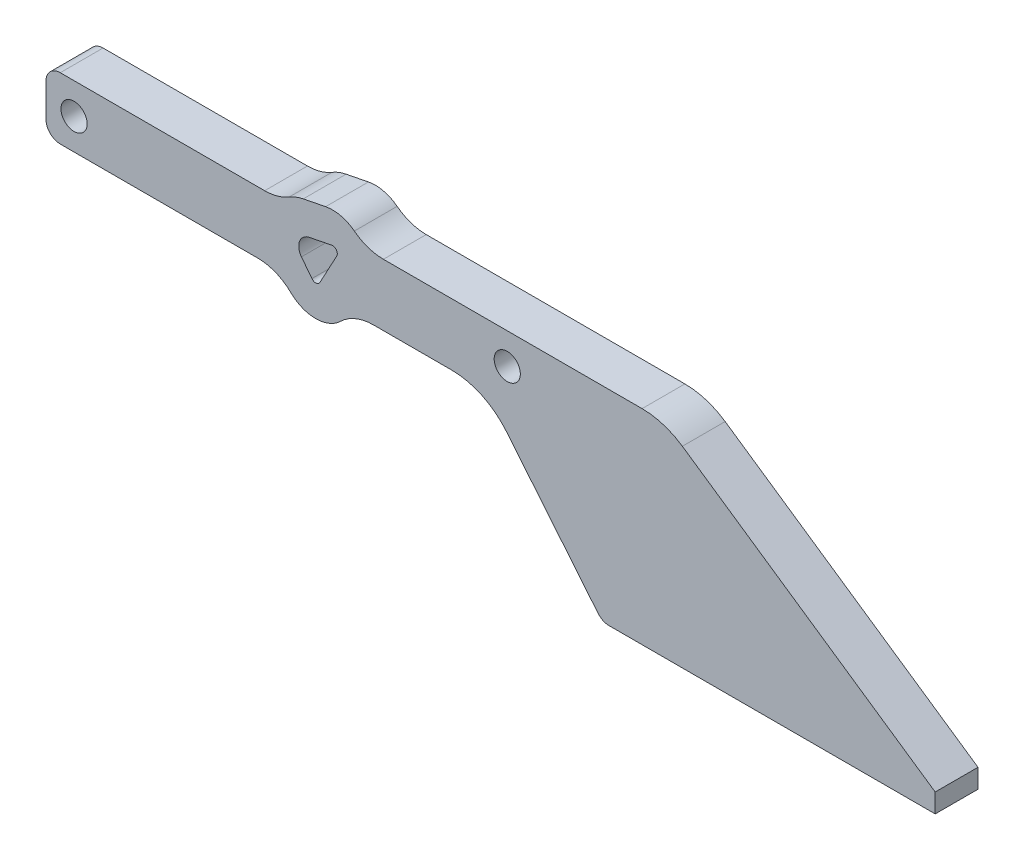
SolidWorks part; units mm, degrees
ref_plane "Front Plane" through (0, 0, 0) normal (0, 0, 1) x (1, 0, 0)
ref_plane "Top Plane" through (0, 0, 0) normal (0, 1, 0) x (1, 0, 0)
ref_plane "Right Plane" through (0, 0, 0) normal (1, 0, 0) x (0, 0, -1)
sketch "Sketch3" plane through (0, 0, 0) normal (0, 0, 1) x (1, 0, 0)
  line L6 (0, 0) -> (-70, 0)
  line L7 (-70, 0) -> (-70, 30) construction
  line L9 (-15.5885, 13) -> (-57, 13) construction
  line L15 (-57, 42.3999) -> (-57, 43) construction
  line L16 (-57, 43) -> (-187, 43)
  line L18 (-90, 30) -> (-90, 43) construction
  line L19 (-90, 36.5) -> (-90, -3.5) construction
  line L20 (-90, -3.5) -> (-131.1, -3.5) construction
  line L21 (-131.1, -3.5) -> (-131.1, 36.5) construction
  line L22 (-131.0771, 31.9631) -> (-133.2788, 34.8221)
  line L23 (-187, 43) -> (-187, 30)
  line L24 (-90, 36.5) -> (-171.1, 36.5) construction
  line L25 (0, 0) -> (0, 4)
  line L26 (0, 4) -> (-15.5885, 13) construction
  line L27 (-126.9314, 40.1288) -> (-131.6341, 39.1976)
  line L28 (0, 13) -> (-57, 13) construction
  line L29 (-125.8571, 38.673) -> (-129.4048, 32.0984)
  line L30 (-120.1367, 35.5862) -> (-123.6844, 29.0117)
  line L31 (-136.227, 27.9972) -> (-138.4287, 30.8562)
  line L32 (-128.1939, 46.505) -> (-132.8967, 45.5738)
  line L35 (-57, 13) -> (-57, 42.3999) construction
  line L36 (-57, 13) -> (-57, 43) construction
  line L37 (-70, 30) -> (-90, 30) construction
  line L38 (-70, 30) -> (-187, 30) construction
  line L39 (-57, 43) -> (0, 4)
  line L41 (-109.2425, 30) -> (-113.8462, 30) construction
  line L42 (-113.8462, 30) -> (-187, 30)
  line L43 (-113.8462, 30) -> (-94.6383, 30)
  line L44 (-94.6383, 30) -> (-70, 0)
  circle A0 centre (-90, 36.5) radius 2.75
  arc A1 (-131.6341, 39.1976) -> (-133.2788, 34.8221) centre (-131.1, 36.5) ccw
  circle A5 centre (-171.1, 36.5) radius 2.75 construction
  circle A6 centre (-181.1, 36.5) radius 2.75
  arc A8 (-120.4263, 35.0496) -> (-109.2425, 30) centre (-131.1, -3.5) ccw construction
  arc A9 (-131.0771, 31.9631) -> (-129.4048, 32.0984) centre (-130.2848, 32.5733) ccw
  arc A10 (-126.9314, 40.1288) -> (-125.8571, 38.673) centre (-126.7371, 39.1478) cw
  arc A11 (-136.227, 27.9972) -> (-123.6844, 29.0117) centre (-130.2848, 32.5733) ccw
  arc A12 (-132.8967, 45.5738) -> (-138.4287, 30.8562) centre (-131.1, 36.5) ccw
  arc A13 (-128.1939, 46.505) -> (-120.1367, 35.5862) centre (-126.7371, 39.1478) cw
  arc A14 (-109.2425, 30) -> (-120.4263, 35.0496) centre (-131.1, -3.5) ccw construction
  circle A15 centre (-191.1, 36.5) radius 2.75 [skipped]
  dimension "D7" = 40
  dimension "D8" = 130
  dimension "D12" = 70
  dimension "D3" = 5.5
  dimension "D14" = 2.75
  dimension "D15" = 1
  dimension "D19" = 91.1
  dimension "D1" = 13
  dimension "D2" = 20
  dimension "D4" = 40
  dimension "D5" = 41.1
  dimension "D9" = 30
  dimension "D10" = 4
  dimension "D11" = 120
  dimension "D13" = 52.4
  dimension "D6" = 11.2
  dimension "D16" = 10
  dimension "D17" = 6.5
  dimension "D18" = 3
extrude "Boss-Extrude3" add sketch "Sketch3" along normal mid plane 9
fillet "Fillet13" radius 15 2 edges at (-57, 43, 0) (-94.6383, 30, 0)
fillet "Fillet14" radius 10 4 edges at (-120.302, 43, 0) (-137.6812, 43, 0) (-137.7693, 30, 0) (-123.1511, 30, 0)
fillet "Fillet15" radius 3 3 edges at (-70, 0, 0) (-187, 43, 0) (-187, 30, 0)
